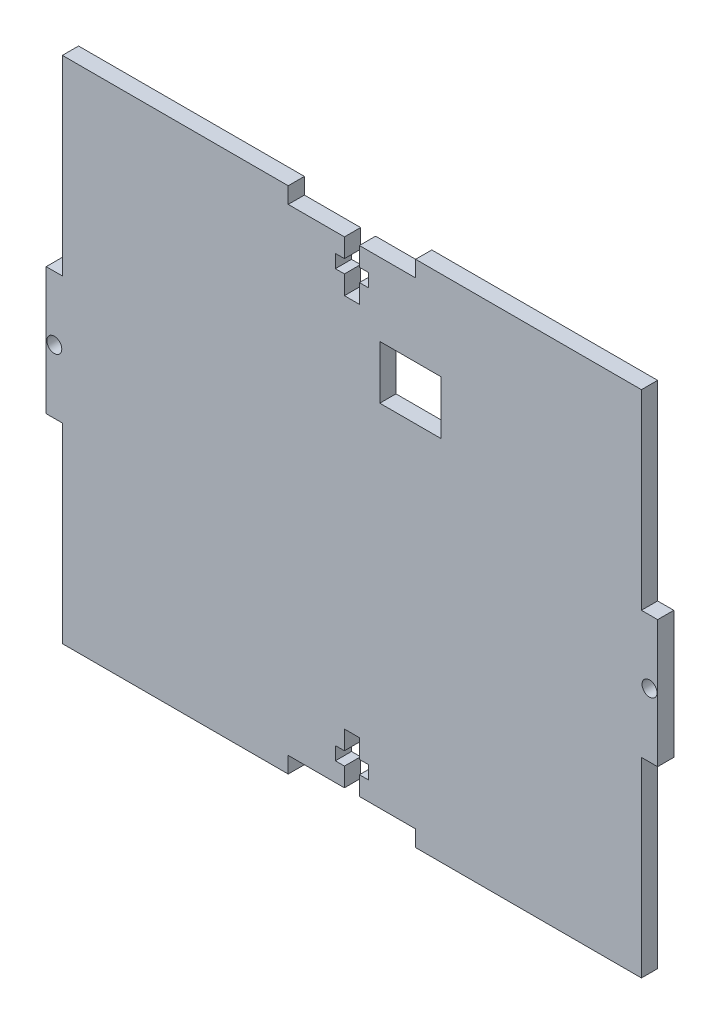
SolidWorks part; units mm, degrees
ref_plane "Front Plane" through (0, 0, 0) normal (0, 0, 1) x (1, 0, 0)
ref_plane "Top Plane" through (0, 0, 0) normal (0, 1, 0) x (1, 0, 0)
ref_plane "Right Plane" through (0, 0, 0) normal (1, 0, 0) x (0, 0, -1)
sketch "Sketch1" plane through (0, 0, 0) normal (0, 0, 1) x (1, 0, 0)
  line L0 (0, 50) -> (0, -50) construction
  line L1 (-56.825, 50) -> (56.825, 50)
  line L2 (-56.825, 50) -> (-56.825, -50)
  line L3 (-56.825, -50) -> (56.825, -50)
  line L4 (56.825, 50) -> (56.825, -50)
  line L5 (-56.825, 50) -> (56.825, -50) construction
  line L6 (-56.825, -50) -> (56.825, 50) construction
  line L7 (-56.825, 0) -> (56.825, 0) construction
  line L8 (-3.25, -40.525) -> (3.25, -40.525)
  line L9 (12.5, 50) -> (-12.5, 50)
  line L10 (12.5, 50) -> (12.5, 46.825)
  line L11 (12.5, 46.825) -> (-12.5, 46.825)
  line L12 (-12.5, 50) -> (-12.5, 46.825)
  line L13 (12.5, 50) -> (-12.5, 46.825) construction
  line L14 (12.5, 46.825) -> (-12.5, 50) construction
  line L15 (-1.47, 46.825) -> (1.47, 46.825)
  line L16 (-1.47, 46.825) -> (-1.47, 36.825)
  line L17 (-1.47, 36.825) -> (1.47, 36.825)
  line L18 (1.47, 46.825) -> (1.47, 36.825)
  line L19 (-1.47, 46.825) -> (1.47, 36.825) construction
  line L20 (-1.47, 36.825) -> (1.47, 46.825) construction
  line L21 (-3.25, 43.125) -> (3.25, 43.125)
  line L22 (-3.25, 43.125) -> (-3.25, 40.525)
  line L23 (-3.25, 40.525) -> (3.25, 40.525)
  line L24 (3.25, 43.125) -> (3.25, 40.525)
  line L25 (-3.25, 43.125) -> (3.25, 40.525) construction
  line L26 (-3.25, 40.525) -> (3.25, 43.125) construction
  line L27 (3.25, -43.125) -> (3.25, -40.525)
  line L28 (-3.25, -43.125) -> (3.25, -43.125)
  line L29 (-3.25, -43.125) -> (-3.25, -40.525)
  line L30 (-1.47, -36.825) -> (1.47, -36.825)
  line L31 (1.47, -46.825) -> (1.47, -36.825)
  line L32 (-1.47, -46.825) -> (1.47, -46.825)
  line L33 (-1.47, -46.825) -> (-1.47, -36.825)
  line L34 (12.5, -46.825) -> (-12.5, -46.825)
  line L35 (-12.5, -50) -> (-12.5, -46.825)
  line L36 (12.5, -50) -> (-12.5, -50)
  line L37 (12.5, -50) -> (12.5, -46.825)
  line L38 (60, -12.5) -> (56.825, -12.5)
  line L39 (-60, 12.5) -> (-56.825, 12.5)
  line L40 (-60, 12.5) -> (-60, -12.5)
  line L41 (-60, -12.5) -> (-56.825, -12.5)
  line L42 (-56.825, 12.5) -> (-56.825, -12.5)
  line L43 (-60, 12.5) -> (-56.825, -12.5) construction
  line L44 (-60, -12.5) -> (-56.825, 12.5) construction
  line L45 (56.825, 12.5) -> (56.825, -12.5)
  line L46 (60, 12.5) -> (56.825, 12.5)
  line L47 (60, 12.5) -> (60, -12.5)
  circle A0 centre (-58.4125, 0) radius 1.47
  circle A1 centre (58.4125, 0) radius 1.47
  point P0 (0, 0)
  point P10 (0, 48.4125)
  point P15 (0, 41.825)
  point P20 (0, 41.825)
  point P37 (-58.4125, 0)
  dimension "D11" = 2.94
  dimension "D1" = 100
  dimension "D2" = 113.65
  dimension "D3" = 3.175
  dimension "D4" = 10
  dimension "D5" = 2.94
  dimension "D6" = 25
  dimension "D7" = 6.5
  dimension "D8" = 2.6
  dimension "D9" = 6.3
  dimension "D10" = 3.175
extrude "Boss-Extrude1" add sketch "Sketch1" along normal mid plane 3.175 contours L21 L24 L23 L18 L17 L16 L22 L11 L12 L1 L2 L3 L4 L10 | L40 L39 L42 L41 | A0 | L38 L45 L46 L47 | A1
sketch "Sketch2" plane through (0, 0, -1.5875) normal (0, 0, -1) x (-1, 0, 0)
  line L0 (-5.975, 32.525) -> (-16.975, 32.525) construction
  line L1 (-17.475, 32.025) -> (-17.475, 22.525) construction
  line L2 (-5.475, 22.525) -> (-5.475, 32.025) construction
  line L3 (-16.975, 22.025) -> (-5.975, 22.025) construction
  line L4 (-5.975, 32.525) -> (-16.975, 32.525)
  line L5 (-17.475, 32.025) -> (-17.475, 22.525)
  line L6 (-5.475, 22.525) -> (-5.475, 32.025)
  line L7 (-16.975, 22.025) -> (-5.975, 22.025)
  line L8 (-17.475, 32.025) -> (-17.475, 32.525)
  line L9 (-17.475, 32.525) -> (-16.975, 32.525)
  line L10 (-5.975, 32.525) -> (-5.475, 32.525)
  line L11 (-5.475, 32.525) -> (-5.475, 32.025)
  line L12 (-5.975, 22.025) -> (-5.475, 22.025)
  line L13 (-5.475, 22.025) -> (-5.475, 22.525)
  line L14 (-17.475, 22.525) -> (-17.475, 22.025)
  line L15 (-17.475, 22.025) -> (-16.975, 22.025)
extrude "Cut-Extrude1" cut sketch "Sketch2" against normal through all
